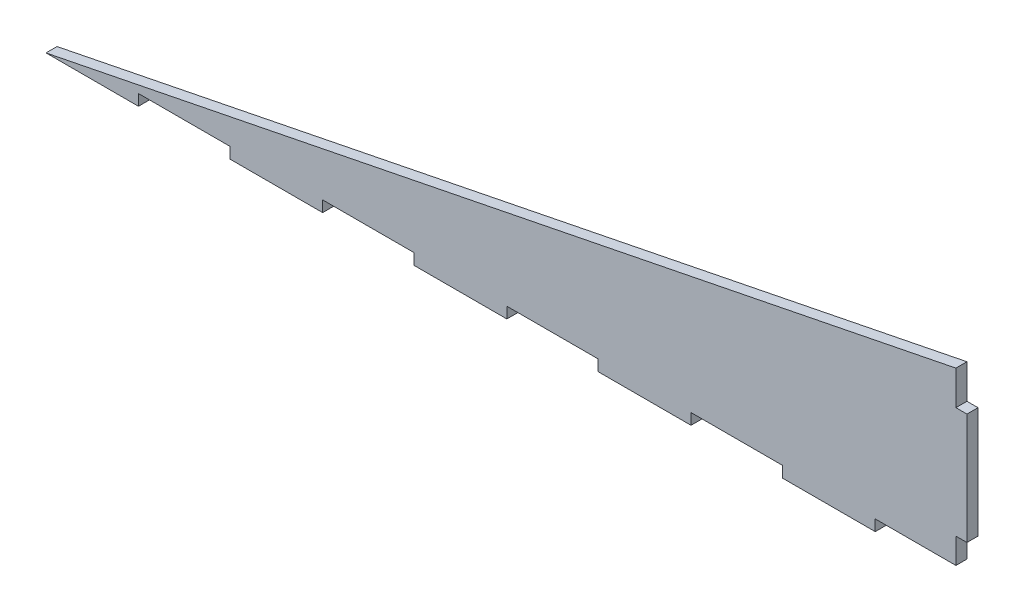
SolidWorks part; units mm, degrees
ref_plane "Front Plane" through (0, 0, 0) normal (0, 0, 1) x (1, 0, 0)
ref_plane "Top Plane" through (0, 0, 0) normal (0, 1, 0) x (1, 0, 0)
ref_plane "Right Plane" through (0, 0, 0) normal (1, 0, 0) x (0, 0, -1)
sketch "Sketch1" plane through (0, 0, 0) normal (0, 0, 1) x (1, 0, 0)
  line L0 (0, 0) -> (250, 50)
  line L1 (0, 0) -> (250, 0)
  line L2 (0, 0) -> (0, 50)
  line L3 (0, 50) -> (250, 50)
  line L4 (250, 0) -> (250, 50)
  line L5 (247, 40.1) -> (247, 49.4)
  line L6 (250, 40.1) -> (247, 40.1)
  line L7 (250, 40.1) -> (250, 9.9)
  line L8 (250, 9.9) -> (247, 9.9)
  line L9 (247, 40.1) -> (247, 9.9)
  line L10 (247, 9.9) -> (247, 0)
  line L11 (75.1, 0) -> (75.1, 3)
  line L12 (25.1, 0) -> (49.9, 0)
  line L13 (25.1, 0) -> (25.1, 3)
  line L14 (25.1, 3) -> (49.9, 3)
  line L15 (49.9, 0) -> (49.9, 3)
  line L16 (75.1, 0) -> (99.9, 0)
  line L17 (99.9, 0) -> (99.9, 3)
  line L18 (75.1, 3) -> (99.9, 3)
  line L19 (125.1, 0) -> (125.1, 3)
  line L20 (125.1, 0) -> (149.9, 0)
  line L21 (149.9, 0) -> (149.9, 3)
  line L22 (125.1, 3) -> (149.9, 3)
  line L23 (175.1, 0) -> (175.1, 3)
  line L24 (175.1, 0) -> (199.9, 0)
  line L25 (199.9, 0) -> (199.9, 3)
  line L26 (175.1, 3) -> (199.9, 3)
  line L27 (225.1, 0) -> (225.1, 3)
  line L28 (225.1, 0) -> (249.9, 0)
  line L29 (249.9, 0) -> (249.9, 3)
  line L30 (225.1, 3) -> (249.9, 3)
  dimension "D1" = 50
  dimension "D2" = 250
  dimension "D3" = 30.2
  dimension "D4" = 9.9
  dimension "D5" = 3
  dimension "D6" = 3
  dimension "D7" = 24.8
  dimension "D8" = 25.1
  dimension "D10" = 25.2
  dimension "D9" = 5
extrude "Boss-Extrude1" add sketch "Sketch1" along normal blind 3 contours L27 L30 L10 L9 L5 L0 L1 L13 L14 L15 L11 L18 L17 L19 L22 L21 L23 L26 L25 | L6 L9 L8 L4
